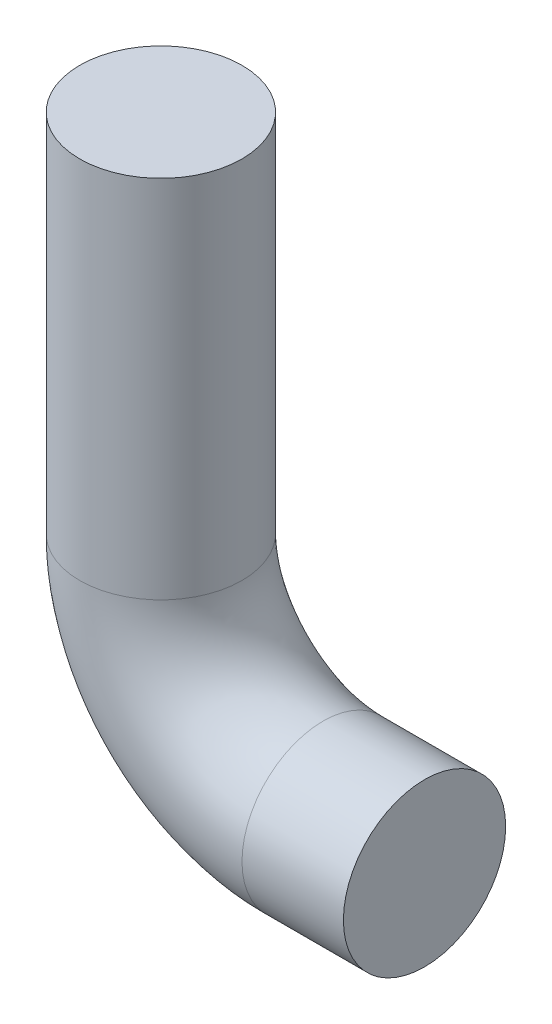
SolidWorks part; units mm, degrees
ref_plane "Front Plane" through (0, 0, 0) normal (0, 0, 1) x (1, 0, 0)
ref_plane "Top Plane" through (0, 0, 0) normal (0, 1, 0) x (1, 0, 0)
ref_plane "Right Plane" through (0, 0, 0) normal (1, 0, 0) x (0, 0, -1)
sketch "Sketch7" plane through (0, 0, 0) normal (0, 0, 1) x (1, 0, 0)
  line L0 (0, 0) -> (-31.75, 0)
  line L1 (55, 0) -> (-55, 0) construction
  line L2 (-82.55, 50.8) -> (-82.55, 165.1)
  arc A0 (-31.75, 0) -> (-82.55, 50.8) centre (-31.75, 50.8) cw
  point P8 (-82.55, 0)
  dimension "D1" = 50.8
  dimension "D2" = 31.75
  dimension "D3" = 114.3
sketch "Sketch8" plane through (0, 0, 0) normal (1, 0, 0) x (0, 0, -1)
  circle A0 centre (0, 0) radius 25.4
  dimension "D1" = 50.8
sweep "Sweep1" add profiles "Sketch8" path "Sketch7"
